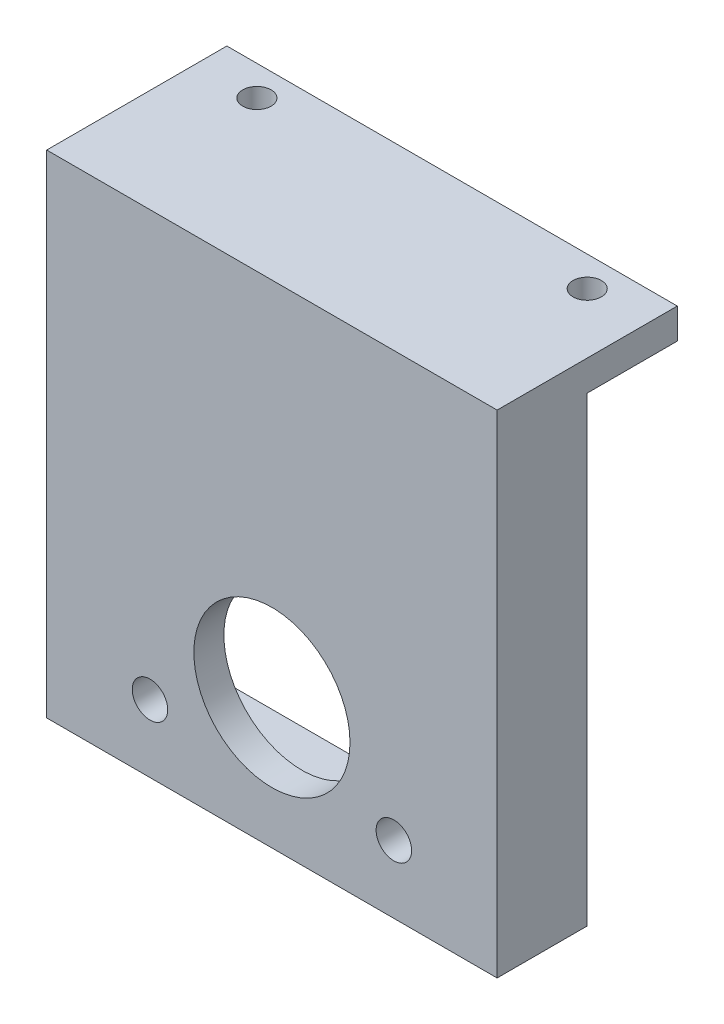
SolidWorks part; units mm, degrees
ref_plane "Front Plane" through (0, 0, 0) normal (0, 0, 1) x (1, 0, 0)
ref_plane "Top Plane" through (0, 0, 0) normal (0, 1, 0) x (1, 0, 0)
ref_plane "Right Plane" through (0, 0, 0) normal (1, 0, 0) x (0, 0, -1)
sketch "Sketch2" plane through (0, 0, 0) normal (0, 0, 1) x (1, 0, 0)
  line L6 (-16.51, 36.5252) -> (-16.51, 2.54)
  line L7 (-16.51, 2.54) -> (16.51, 2.54)
  line L8 (16.51, 2.54) -> (16.51, 36.5252)
  line L9 (19.05, 41.6052) -> (19.05, 0)
  line L10 (-19.05, 0) -> (19.05, 0)
  line L11 (-19.05, 41.6052) -> (-19.05, 0)
  line L13 (-19.05, 41.6052) -> (19.05, 41.6052)
  line L14 (-16.51, 36.5252) -> (16.51, 36.5252)
extrude "Boss-Extrude1" add sketch "Sketch2" along normal blind 5.08
sketch "Sketch4" plane through (0, 0, 0) normal (0, 0, -1) x (-1, 0, 0)
  line L0 (-19.05, 41.6052) -> (19.05, 41.6052) construction
  line L1 (-19.05, 41.6052) -> (19.05, 41.6052)
  line L2 (-19.05, 41.6052) -> (-19.05, 39.0362)
  line L3 (-19.05, 0) -> (-19.05, 41.6052) construction
  line L4 (-19.05, 39.0362) -> (19.05, 39.0652)
  line L5 (19.05, 41.6052) -> (19.05, 0) construction
  line L7 (19.05, 39.0652) -> (19.05, 41.6052)
extrude "Boss-Extrude2" add sketch "Sketch4" along normal blind 7.62
hole_wizard "M2 Clearance Hole1" positions "Sketch5" profile "Sketch6" hole size "M2" standard "ANSI Metric" end condition through all
sketch "Sketch5" plane through (0, 41.6052, 0) normal (0, 1, 0) x (1, 0, 0)
  line L0 (19.05, 0) -> (-19.05, 0) construction
  line L1 (19.05, -5.08) -> (19.05, 7.62) construction
  line L2 (-19.05, -5.08) -> (-19.05, 7.62) construction
  line L4 (-13.97, 5.08) -> (13.97, 5.08) construction
  point P0 (-13.97, 5.08)
  point P2 (13.97, 5.08)
  point P18 (0, 5.08)
  point P19 (0, 0)
  dimension "D1" = 5.08
  dimension "D2" = 5.08
sketch "Sketch6" plane through (-13.97, 41.6052, -5.08) normal (1, 0, 0) x (0, 0, 1)
  line L0 (0, 0) -> (0, 41.6052)
  line L1 (0, 41.6052) -> (1.2, 41.6052)
  line L2 (1.2, 41.6052) -> (1.2, 0)
  line L5 (1.2, 0) -> (0, 0)
  line L11 (0, -6.35) -> (0, 107.95) construction
  dimension "Thru Hole Dia." = 2.4
  dimension "Thru Hole Depth" = 41.6052
sketch "Sketch7" plane through (0, 0, 5.08) normal (0, 0, 1) x (1, 0, 0)
  line L12 (-10.3149, 5.715) -> (10.3149, 5.715) construction
  line L13 (-19.05, 0) -> (19.05, 0) construction
  circle A0 centre (-10.3149, 5.715) radius 1.5011
  circle A1 centre (10.3149, 5.715) radius 1.5011
  point P13 (0, 5.715)
  dimension "D1" = 3.0023
  dimension "D3" = 20.6299
  dimension "D2" = 5.715
sketch "Sketch8" plane through (0, 0, 5.08) normal (0, 0, 1) x (1, 0, 0)
  line L1 (0, 11.0261) -> (0, 0) construction
  line L2 (-16.51, 4.4221) -> (16.51, 4.4221) construction
  line L3 (-16.51, 36.5252) -> (-16.51, 2.54) construction
  line L4 (16.51, 2.54) -> (16.51, 36.5252) construction
  line L5 (-19.05, 0) -> (19.05, 0) construction
  line L6 (19.05, 0) -> (19.05, 41.6052) construction
  line L7 (19.05, 41.6052) -> (-19.05, 41.6052) construction
  line L8 (-19.05, 41.6052) -> (-19.05, 0) construction
  line L9 (-19.05, 0) -> (19.05, 0)
  line L10 (19.05, 0) -> (19.05, 41.6052)
  line L11 (19.05, 41.6052) -> (-19.05, 41.6052)
  line L12 (-19.05, 41.6052) -> (-19.05, 0)
  circle A0 centre (0, 11.0261) radius 6.604
  dimension "D1" = 13.208
  dimension "D2" = 11.0261
extrude "Boss-Extrude3" add sketch "Sketch8" along normal blind 2.54
extrude "Cut-Extrude1" cut sketch "Sketch7" against normal through all both and the other way through all
sketch "Sketch9" plane through (0, 0, 7.62) normal (0, 0, 1) x (1, 0, 0)
  circle A1 centre (0, 11.0261) radius 6.604 construction
  circle A2 centre (0, 11.0261) radius 7.874
  circle A3 centre (0, 11.0261) radius 7.874
  circle A4 centre (0, 11.0261) radius 6.604
  dimension "D1" = 1.27
extrude "Boss-Extrude4" [suppressed] add sketch "Sketch9" along normal blind 3.38
equation "\"D1@Sketch7\"=2*0.0591in"
equation "\"D1@Boss-Extrude4\"=0.25in-2.97mm"
